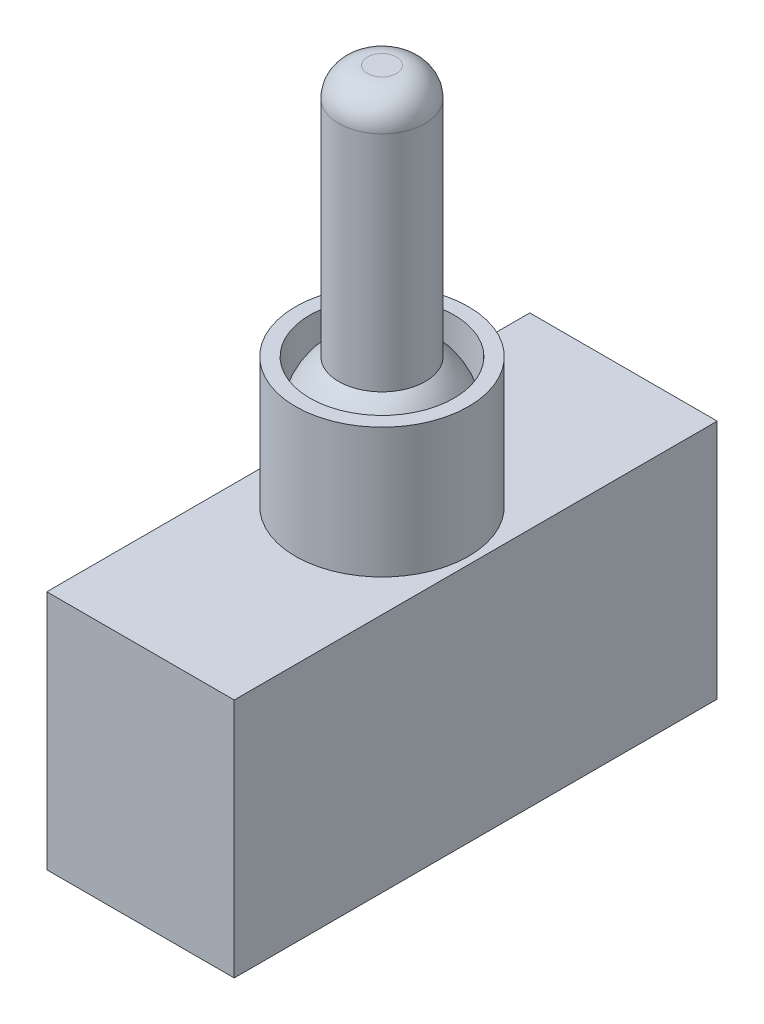
SolidWorks part; units mm, degrees
ref_plane "Спереди" through (0, 0, 0) normal (0, 0, 1) x (1, 0, 0)
ref_plane "Сверху" through (0, 0, 0) normal (0, 1, 0) x (1, 0, 0)
ref_plane "Справа" through (0, 0, 0) normal (1, 0, 0) x (0, 0, -1)
sketch "Sketch1" plane through (0, 0, 0) normal (0, 1, 0) x (1, 0, 0)
  line L1 (6.5, -16.75) -> (-6.5, -16.75)
  line L2 (6.5, -16.75) -> (6.5, 16.75)
  line L3 (6.5, 16.75) -> (-6.5, 16.75)
  line L4 (-6.5, -16.75) -> (-6.5, 16.75)
  line L5 (6.5, -16.75) -> (-6.5, 16.75) construction
  line L6 (6.5, 16.75) -> (-6.5, -16.75) construction
  point P0 (0, 0)
  dimension "D1" = 13
  dimension "D2" = 33.5
extrude "Boss-Extrude1" add sketch "Sketch1" along normal blind 16.7
sketch "Sketch2" plane through (0, 16.7, 0) normal (0, 1, 0) x (1, 0, 0)
  line L0 (-6.5, 16.75) -> (6.5, -16.75) construction
  circle A0 centre (0, 0) radius 6
  dimension "D1" = 12
extrude "Boss-Extrude2" add sketch "Sketch2" along normal blind 9
sketch "Sketch4" plane through (0, 25.7, 0) normal (0, 1, 0) x (1, 0, 0)
  circle A0 centre (0, 0) radius 5
  dimension "D1" = 10
extrude "Cut-Extrude1" cut sketch "Sketch4" against normal blind 4
sketch "Sketch5" plane through (0, 21.7, 0) normal (0, 1, 0) x (1, 0, 0)
  circle A0 centre (0, 0) radius 3
  dimension "D1" = 6
extrude "Boss-Extrude3" add sketch "Sketch5" along normal blind 21.5
sketch "Sketch3" plane through (0, 21.7, 0) normal (0, 1, 0) x (1, 0, 0)
  line L0 (0, -6) -> (0, 6) construction
  line L1 (0, -5) -> (0, 5)
  circle A0 centre (0, 0) radius 6 construction
  arc A1 (0, -5) -> (0, 5) centre (0, 0) cw
  point P7 (0, 0)
  dimension "D1" = 10
revolve "Revolve2" add sketch "Sketch3" angle 180 about L0
fillet "Fillet1" radius 2 1 edges at (0, 43.2, 3)
